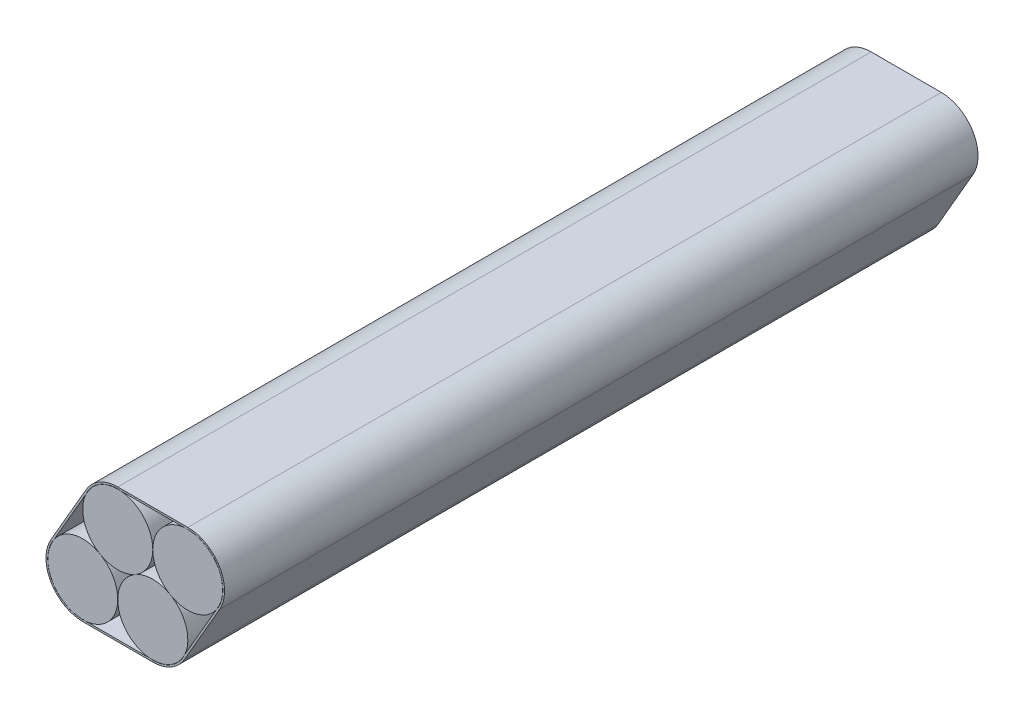
SolidWorks part; units mm, degrees
material "1060 Сплав"
ref_plane "Спереди" through (0, 0, 0) normal (0, 0, 1) x (1, 0, 0)
ref_plane "Сверху" through (0, 0, 0) normal (0, 1, 0) x (1, 0, 0)
ref_plane "Справа" through (0, 0, 0) normal (1, 0, 0) x (0, 0, -1)
sketch "Эскиз1" plane through (0, 0, 0) normal (0, 0, 1) x (1, 0, 0)
  line L0 (9.3, 25.3581) -> (27.9, 25.3581)
  line L1 (35.9107, 11.4831) -> (26.6107, -4.625)
  line L2 (18.6, -9.25) -> (0, -9.25)
  line L3 (-8.0107, 4.625) -> (1.2893, 20.7331)
  line L4 (9.3, 25.8581) -> (27.9, 25.8581)
  line L5 (36.3437, 11.2331) -> (27.0437, -4.875)
  line L6 (18.6, -9.75) -> (0, -9.75)
  line L7 (-8.4437, 4.875) -> (0.8563, 20.9831)
  circle A0 centre (0, 0) radius 9.3
  circle A1 centre (18.6, 0) radius 9.3
  circle A2 centre (9.3, 16.1081) radius 9.3
  circle A3 centre (27.9, 16.1081) radius 9.3
  arc A4 (27.9, 25.3581) -> (35.9107, 11.4831) centre (27.9, 16.1081) cw
  arc A5 (1.2893, 20.7331) -> (9.3, 25.3581) centre (9.3, 16.1081) cw
  arc A6 (0, -9.25) -> (-8.0107, 4.625) centre (0, 0) cw
  arc A7 (18.6, -9.25) -> (26.6107, -4.625) centre (18.6, 0) ccw
  arc A8 (27.9, 25.8581) -> (36.3437, 11.2331) centre (27.9, 16.1081) cw
  arc A9 (18.6, -9.75) -> (27.0437, -4.875) centre (18.6, 0) ccw
  arc A10 (0, -9.75) -> (-8.4437, 4.875) centre (0, 0) cw
  arc A11 (0.8563, 20.9831) -> (9.3, 25.8581) centre (9.3, 16.1081) cw
  dimension "D1" = 18.6
  dimension "D3" = 9.25
  dimension "D2" = 0.5
extrude "Бобышка-Вытянуть1" add sketch "Эскиз1" along normal blind 200 contours A0 | A2 | A3 | A1 | A11 L7 A10 L6 A9 L5 A8 L4 A7 L2 A6 L3 A5 L0 A4 L1
